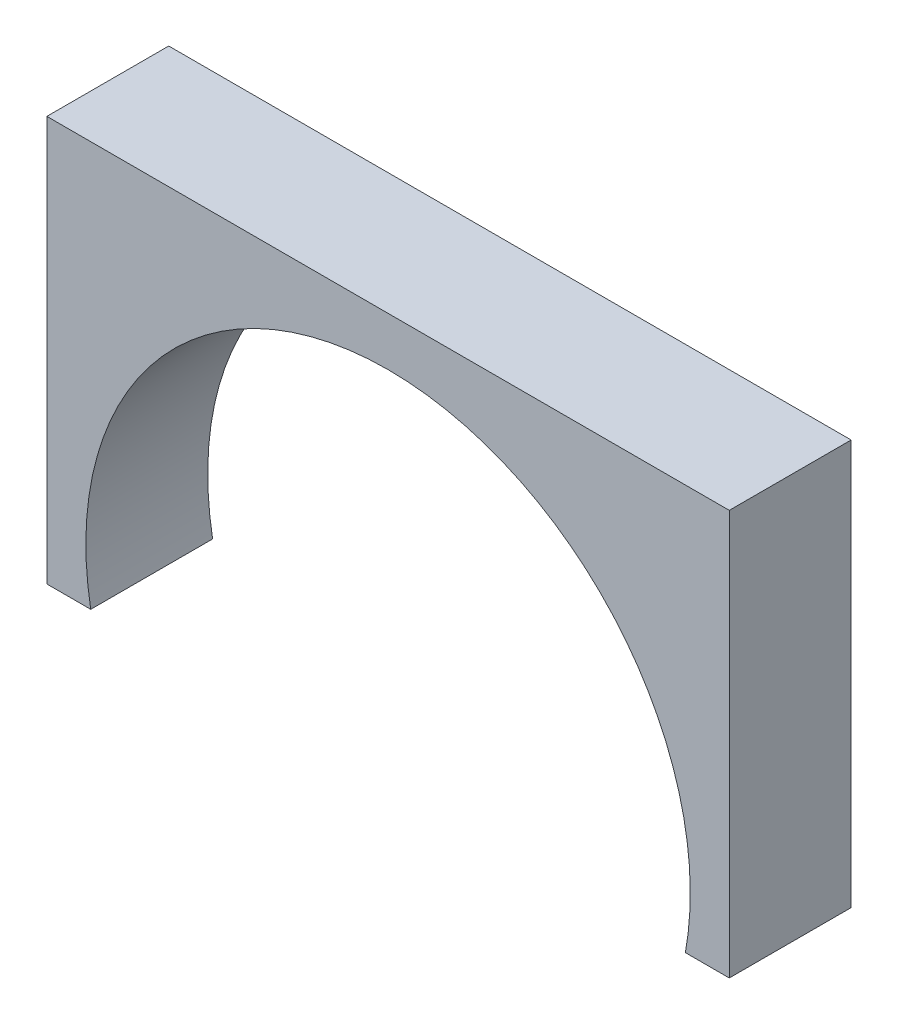
SolidWorks part; units mm, degrees
ref_plane "Front Plane" through (0, 0, 0) normal (0, 0, 1) x (1, 0, 0)
ref_plane "Top Plane" through (0, 0, 0) normal (0, 1, 0) x (1, 0, 0)
ref_plane "Right Plane" through (0, 0, 0) normal (1, 0, 0) x (0, 0, -1)
sketch "Sketch1" plane through (0, 0, 0) normal (0, 0, 1) x (1, 0, 0)
  line L6 (0, 72) -> (0, -11.0905) construction
  line L7 (-70, 72) -> (-70, -11.0905)
  line L10 (70, 72) -> (70, -11.0905)
  line L12 (-61, -11.0905) -> (61, -11.0905) construction
  line L13 (-61, -11.0905) -> (-70, -11.0905)
  line L14 (61, -11.0905) -> (70, -11.0905)
  line L15 (-70, 72) -> (70, 72)
  arc A2 (61, -11.0905) -> (-61, -11.0905) centre (0, 0) ccw
  point P12 (0, 62)
  dimension "D1" = 62
  dimension "D3" = 70
  dimension "D4" = 122
  dimension "D2" = 70
  dimension "D5" = 10
extrude "Boss-Extrude1" add sketch "Sketch1" along normal blind 25
